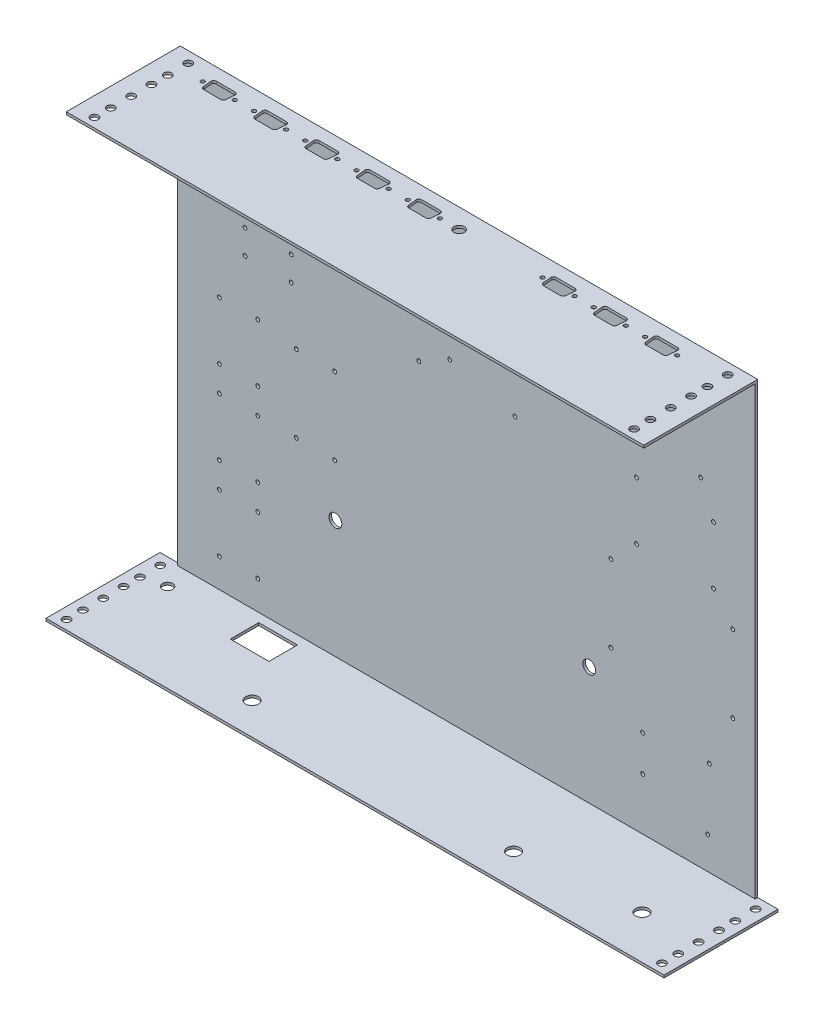
SolidWorks part; units mm, degrees
ref_plane "Front Plane" through (0, 0, 0) normal (0, 0, 1) x (1, 0, 0)
ref_plane "Top Plane" through (0, 0, 0) normal (0, 1, 0) x (1, 0, 0)
ref_plane "Right Plane" through (0, 0, 0) normal (1, 0, 0) x (0, 0, -1)
sketch "Sketch1" plane through (0, 0, 0) normal (0, 0, 1) x (1, 0, 0)
  line L13 (-225.2, -176) -> (225.2, -176)
  line L14 (-225.2, -176) -> (-225.2, 176)
  line L19 (-225.2, 176) -> (225.2, 176)
  line L20 (225.2, -176) -> (225.2, 176)
  line L21 (-225.2, -176) -> (225.2, 176) construction
  line L22 (-225.2, 176) -> (225.2, -176) construction
  point P0 (0, 0)
  dimension "D1" = 450.4
  dimension "D2" = 352
extrude "Boss-Extrude1" add sketch "Sketch1" along normal blind 2
sketch "Sketch4" plane through (0, -176, 0) normal (0, -1, 0) x (1, 0, 0)
  line L0 (-225.2, 2) -> (-225.2, 0) construction
  line L1 (-241, 0) -> (241, 0)
  line L2 (-241, 0) -> (-241, 88.9)
  line L3 (-241, 88.9) -> (241, 88.9)
  line L4 (241, 0) -> (241, 88.9)
  line L5 (225.2, 2) -> (225.2, 0) construction
  line L6 (-227.45, 88.9) -> (-227.45, 0) construction
  line L7 (-236.95, 64.2) -> (-227.45, 64.2)
  line L8 (-236.95, 86.4) -> (-227.45, 86.4)
  line L9 (-236.95, 86.4) -> (-236.95, 76.9)
  line L10 (-236.95, 76.9) -> (-227.45, 76.9)
  line L11 (-227.45, 86.4) -> (-227.45, 76.9)
  line L12 (-236.95, 73.7) -> (-236.95, 64.2)
  line L13 (-236.95, 73.7) -> (-227.45, 73.7)
  line L14 (-227.45, 73.7) -> (-227.45, 64.2)
  line L27 (0, 0) -> (0, 101.053) construction
  line L40 (227.45, 73.7) -> (227.45, 64.2)
  line L41 (236.95, 64.2) -> (227.45, 64.2)
  line L42 (236.95, 73.7) -> (227.45, 73.7)
  line L43 (236.95, 73.7) -> (236.95, 64.2)
  line L44 (227.45, 86.4) -> (227.45, 76.9)
  line L45 (236.95, 86.4) -> (227.45, 86.4)
  line L46 (236.95, 86.4) -> (236.95, 76.9)
  line L47 (236.95, 76.9) -> (227.45, 76.9)
  line L48 (-236.95, 51.5) -> (-227.45, 51.5) [skipped]
  line L49 (-236.95, 61) -> (-236.95, 51.5) [skipped]
  line L50 (-236.95, 61) -> (-227.45, 61) [skipped]
  line L51 (-227.45, 61) -> (-227.45, 51.5) [skipped]
  line L52 (-236.95, 38.8) -> (-227.45, 38.8) [skipped]
  line L53 (-236.95, 48.3) -> (-236.95, 38.8) [skipped]
  line L54 (-236.95, 48.3) -> (-227.45, 48.3) [skipped]
  line L55 (-227.45, 48.3) -> (-227.45, 38.8) [skipped]
  line L56 (-236.95, 26.1) -> (-227.45, 26.1) [skipped]
  line L57 (-236.95, 35.6) -> (-236.95, 26.1) [skipped]
  line L58 (-236.95, 35.6) -> (-227.45, 35.6) [skipped]
  line L59 (-227.45, 35.6) -> (-227.45, 26.1) [skipped]
  line L60 (-236.95, 57.82) -> (-236.95, 48.32)
  line L61 (-236.95, 57.82) -> (-227.45, 57.82)
  line L62 (-227.45, 57.82) -> (-227.45, 48.32)
  line L63 (-236.95, 48.32) -> (-227.45, 48.32)
  line L72 (236.95, 48.32) -> (227.45, 48.32)
  line L73 (227.45, 57.82) -> (227.45, 48.32)
  line L74 (236.95, 57.82) -> (227.45, 57.82)
  line L75 (236.95, 57.82) -> (236.95, 48.32)
  line L92 (-236.95, 45.12) -> (-227.45, 45.12) [skipped]
  line L93 (-227.45, 45.12) -> (-227.45, 35.62) [skipped]
  line L94 (-236.95, 35.62) -> (-227.45, 35.62) [skipped]
  line L95 (-236.95, 45.12) -> (-236.95, 35.62) [skipped]
  line L96 (-236.95, 29.24) -> (-236.95, 19.74) [skipped]
  line L97 (-236.95, 29.24) -> (-227.45, 29.24) [skipped]
  line L98 (-227.45, 29.24) -> (-227.45, 19.74) [skipped]
  line L99 (-236.95, 19.74) -> (-227.45, 19.74) [skipped]
  line L100 (-236.95, 16.54) -> (-227.45, 16.54) [skipped]
  line L101 (-227.45, 16.54) -> (-227.45, 7.04) [skipped]
  line L102 (-236.95, 7.04) -> (-227.45, 7.04) [skipped]
  line L103 (-236.95, 16.54) -> (-236.95, 7.04) [skipped]
  line L104 (236.95, 45.12) -> (236.95, 35.62) [skipped]
  line L105 (236.95, 45.12) -> (227.45, 45.12) [skipped]
  line L106 (227.45, 45.12) -> (227.45, 35.62) [skipped]
  line L107 (236.95, 35.62) -> (227.45, 35.62) [skipped]
  line L108 (236.95, 16.54) -> (236.95, 7.04) [skipped]
  line L109 (236.95, 16.54) -> (227.45, 16.54) [skipped]
  line L110 (227.45, 16.54) -> (227.45, 7.04) [skipped]
  line L111 (236.95, 7.04) -> (227.45, 7.04) [skipped]
  line L112 (236.95, 19.74) -> (227.45, 19.74) [skipped]
  line L113 (227.45, 29.24) -> (227.45, 19.74) [skipped]
  line L114 (236.95, 29.24) -> (227.45, 29.24) [skipped]
  line L115 (236.95, 29.24) -> (236.95, 19.74) [skipped]
  line L116 (-236.95, 41.94) -> (-236.95, 32.44)
  line L117 (-236.95, 41.94) -> (-227.45, 41.94)
  line L118 (-227.45, 41.94) -> (-227.45, 32.44)
  line L119 (-236.95, 32.44) -> (-227.45, 32.44)
  line L120 (-236.95, 29.24) -> (-227.45, 29.24)
  line L121 (-227.45, 29.24) -> (-227.45, 19.74)
  line L122 (-236.95, 19.74) -> (-227.45, 19.74)
  line L123 (-236.95, 29.24) -> (-236.95, 19.74)
  line L124 (-236.95, 13.36) -> (-236.95, 3.86)
  line L125 (-236.95, 3.86) -> (-227.45, 3.86)
  line L126 (-227.45, 13.36) -> (-227.45, 3.86)
  line L127 (-236.95, 13.36) -> (-227.45, 13.36)
  line L128 (227.45, 41.94) -> (227.45, 32.44)
  line L129 (236.95, 32.44) -> (227.45, 32.44)
  line L130 (236.95, 41.94) -> (236.95, 32.44)
  line L131 (236.95, 41.94) -> (227.45, 41.94)
  line L132 (236.95, 29.24) -> (236.95, 19.74)
  line L133 (236.95, 19.74) -> (227.45, 19.74)
  line L134 (227.45, 29.24) -> (227.45, 19.74)
  line L135 (236.95, 29.24) -> (227.45, 29.24)
  line L136 (236.95, 13.36) -> (227.45, 13.36)
  line L137 (236.95, 13.36) -> (236.95, 3.86)
  line L138 (236.95, 3.86) -> (227.45, 3.86)
  line L139 (227.45, 13.36) -> (227.45, 3.86)
  point P21 (-232.2, 57.82)
  dimension "D1" = 15.8
  dimension "D2" = 15.8
  dimension "D3" = 88.9
  dimension "D4" = 2.25
  dimension "D5" = 9.5
  dimension "D6" = 2.5
  dimension "D7" = 9.5
  dimension "D9" = 12.7
  dimension "D11" = 6.38
  dimension "D12" = 2
  dimension "D13" = 6.38
  dimension "D8" = 5
  dimension "D10" = 3
extrude "Boss-Extrude4" add sketch "Sketch4" against normal blind 2
ref_plane "Plane1" through (0, 0, 0) normal (0, 1, 0) x (1, 0, 0)
mirror "Mirror1" about plane through (0, 0, 0) normal (0, 1, 0) of "Boss-Extrude4"
sketch "Sketch5" plane through (0, 176, 0) normal (0, 1, 0) x (1, 0, 0)
  line L0 (-225.2, 0) -> (-225.2, -88.9) construction
  line L1 (241, 0) -> (-241, 0) construction
  line L2 (241, -88.9) -> (-241, -88.9) construction
  line L7 (0, -48.895) -> (0, 48.895) construction
  line L11 (-225.2, 0) -> (-241, 0)
  line L12 (-225.2, 0) -> (-225.2, -88.9)
  line L13 (-225.2, -88.9) -> (-241, -88.9)
  line L14 (-241, 0) -> (-241, -88.9)
  line L15 (225.2, 0) -> (241, 0)
  line L16 (241, 0) -> (241, -88.9)
  line L17 (225.2, -88.9) -> (241, -88.9)
  line L18 (225.2, 0) -> (225.2, -88.9)
extrude "Cut-Extrude2" cut sketch "Sketch5" against normal up to next
sketch "Sketch6" plane through (0, 176, 0) normal (0, 1, 0) x (1, 0, 0)
  line L0 (-225.2, -88.9) -> (-225.2, 0) construction
  line L1 (-215.2, -3.86) -> (-205.7, -3.86)
  line L2 (-215.2, -3.86) -> (-215.2, -13.36)
  line L3 (-215.2, -13.36) -> (-205.7, -13.36)
  line L4 (-205.7, -3.86) -> (-205.7, -13.36)
  line L5 (225.2, 0) -> (-225.2, 0) construction
  line L6 (-215.2, -19.74) -> (-215.2, -29.24)
  line L7 (-215.2, -19.74) -> (-205.7, -19.74)
  line L8 (-215.2, -29.24) -> (-205.7, -29.24)
  line L9 (-205.7, -19.74) -> (-205.7, -29.24)
  line L22 (0, -48.895) -> (0, 48.895) construction
  line L35 (215.2, -3.86) -> (215.2, -13.36)
  line L36 (215.2, -3.86) -> (205.7, -3.86)
  line L37 (205.7, -3.86) -> (205.7, -13.36)
  line L38 (215.2, -13.36) -> (205.7, -13.36)
  line L39 (215.2, -19.74) -> (215.2, -29.24)
  line L40 (215.2, -29.24) -> (205.7, -29.24)
  line L41 (205.7, -19.74) -> (205.7, -29.24)
  line L42 (215.2, -19.74) -> (205.7, -19.74)
  line L43 (-215.2, -76.9) -> (-215.2, -86.4)
  line L44 (-215.2, -35.62) -> (-215.2, -45.12) [skipped]
  line L45 (-215.2, -35.62) -> (-205.7, -35.62) [skipped]
  line L46 (-215.2, -45.12) -> (-205.7, -45.12) [skipped]
  line L47 (-205.7, -35.62) -> (-205.7, -45.12) [skipped]
  line L48 (-215.2, -51.5) -> (-215.2, -61) [skipped]
  line L49 (-215.2, -51.5) -> (-205.7, -51.5) [skipped]
  line L50 (-215.2, -61) -> (-205.7, -61) [skipped]
  line L51 (-205.7, -51.5) -> (-205.7, -61) [skipped]
  line L52 (-215.2, -67.38) -> (-215.2, -76.88) [skipped]
  line L53 (-215.2, -67.38) -> (-205.7, -67.38) [skipped]
  line L54 (-205.7, -67.38) -> (-205.7, -76.88) [skipped]
  line L55 (-215.2, -76.88) -> (-205.7, -76.88) [skipped]
  line L56 (-215.2, -32.44) -> (-215.2, -41.94)
  line L57 (-215.2, -41.94) -> (-205.7, -41.94)
  line L58 (-215.2, -32.44) -> (-205.7, -32.44)
  line L63 (-205.7, -32.44) -> (-205.7, -41.94)
  line L64 (205.7, -32.44) -> (205.7, -41.94)
  line L65 (215.2, -41.94) -> (205.7, -41.94)
  line L66 (215.2, -32.44) -> (215.2, -41.94)
  line L67 (215.2, -32.44) -> (205.7, -32.44)
  line L88 (-215.2, -48.32) -> (-205.7, -48.32) [skipped]
  line L89 (-215.2, -48.32) -> (-215.2, -57.82) [skipped]
  line L90 (-215.2, -57.82) -> (-205.7, -57.82) [skipped]
  line L91 (-205.7, -48.32) -> (-205.7, -57.82) [skipped]
  line L92 (-215.2, -61.02) -> (-215.2, -70.52) [skipped]
  line L93 (-215.2, -70.52) -> (-205.7, -70.52) [skipped]
  line L94 (-215.2, -61.02) -> (-205.7, -61.02) [skipped]
  line L95 (-215.2, -76.9) -> (-205.7, -76.9) [skipped]
  line L96 (-215.2, -76.9) -> (-215.2, -86.4) [skipped]
  line L97 (-215.2, -86.4) -> (-205.7, -86.4) [skipped]
  line L98 (-205.7, -76.9) -> (-205.7, -86.4) [skipped]
  line L99 (-205.7, -61.02) -> (-205.7, -70.52) [skipped]
  line L100 (215.2, -57.82) -> (205.7, -57.82) [skipped]
  line L101 (205.7, -48.32) -> (205.7, -57.82) [skipped]
  line L102 (215.2, -48.32) -> (205.7, -48.32) [skipped]
  line L103 (215.2, -48.32) -> (215.2, -57.82) [skipped]
  line L104 (205.7, -61.02) -> (205.7, -70.52) [skipped]
  line L105 (215.2, -70.52) -> (205.7, -70.52) [skipped]
  line L106 (215.2, -61.02) -> (215.2, -70.52) [skipped]
  line L107 (215.2, -61.02) -> (205.7, -61.02) [skipped]
  line L108 (215.2, -86.4) -> (205.7, -86.4) [skipped]
  line L109 (205.7, -76.9) -> (205.7, -86.4) [skipped]
  line L110 (215.2, -76.9) -> (205.7, -76.9) [skipped]
  line L111 (215.2, -76.9) -> (215.2, -86.4) [skipped]
  line L112 (-215.2, -76.9) -> (-205.7, -76.9)
  line L113 (-215.2, -86.4) -> (-205.7, -86.4)
  line L114 (-205.7, -76.9) -> (-205.7, -86.4)
  line L115 (-205.7, -64.2) -> (-205.7, -73.7)
  line L116 (-215.2, -73.7) -> (-205.7, -73.7)
  line L117 (-215.2, -64.2) -> (-215.2, -73.7)
  line L118 (-215.2, -64.2) -> (-205.7, -64.2)
  line L119 (-215.2, -57.82) -> (-205.7, -57.82)
  line L120 (-215.2, -48.32) -> (-215.2, -57.82)
  line L121 (-215.2, -48.32) -> (-205.7, -48.32)
  line L122 (-205.7, -48.32) -> (-205.7, -57.82)
  line L123 (205.7, -48.32) -> (205.7, -57.82)
  line L124 (215.2, -57.82) -> (205.7, -57.82)
  line L125 (215.2, -48.32) -> (215.2, -57.82)
  line L126 (215.2, -48.32) -> (205.7, -48.32)
  line L127 (215.2, -64.2) -> (205.7, -64.2)
  line L128 (215.2, -64.2) -> (215.2, -73.7)
  line L129 (215.2, -73.7) -> (205.7, -73.7)
  line L130 (205.7, -64.2) -> (205.7, -73.7)
  line L131 (215.2, -76.9) -> (205.7, -76.9)
  line L132 (205.7, -76.9) -> (205.7, -86.4)
  line L133 (215.2, -86.4) -> (205.7, -86.4)
  line L134 (215.2, -76.9) -> (215.2, -86.4)
  dimension "D1" = 9.5
  dimension "D2" = 9.5
  dimension "D3" = 10
  dimension "D4" = 3.86
  dimension "D6" = 6.38
  dimension "D8" = 3.2
  dimension "D10" = 6.38
  dimension "D5" = 5
  dimension "D7" = 3
  dimension "D9" = 2
extrude "Cut-Extrude3" cut sketch "Sketch6" against normal up to next
sketch "Sketch9" plane through (0, 0, 2) normal (0, 0, 1) x (1, 0, 0)
  line L0 (-87.2, -174) -> (-87.2, 8) construction
  line L1 (241, -174) -> (-241, -174) construction
  line L2 (80.8, -174) -> (80.8, 8) construction
  line L3 (-225.2, -174) -> (225.2, -174) construction
  line L4 (-87.2, 8) -> (80.8, 8) construction
  line L5 (-225.2, 174) -> (-225.2, -174) construction
  circle A0 centre (-102.2, -82) radius 5
  circle A3 centre (95.8, -82) radius 5
  dimension "D4" = 15
  dimension "D5" = 10
  dimension "D6" = 10
  dimension "D1" = 138
  dimension "D2" = 168
  dimension "D3" = 182
  dimension "D8" = 15
  dimension "D9" = 90
  dimension "D15" = 90
extrude "Cut-Extrude4" cut sketch "Sketch9" against normal up to next
sketch "Sketch11" plane through (0, -176, 0) normal (0, -1, 0) x (1, 0, 0)
  line L0 (-90.2, 0) -> (-90.2, 85.1375) construction
  line L1 (-241, 0) -> (241, 0) construction
  line L2 (83.8, 0) -> (83.8, 87.0276) construction
  line L10 (-241, 88.9) -> (-241, 0) construction
  line L11 (-90.2, 79) -> (83.8, 79) construction
  circle A0 centre (-105.2, 64) radius 5
  circle A1 centre (98.8, 64) radius 5
  dimension "D4" = 10
  dimension "D5" = 10
  dimension "D1" = 174
  dimension "D2" = 150.8
  dimension "D3" = 79
  dimension "D6" = 15
  dimension "D7" = 15
  dimension "D8" = 15
  dimension "D9" = 15
extrude "Cut-Extrude5" cut sketch "Sketch11" against normal up to next
sketch "Sketch12" plane through (0, 0, 2) normal (0, 0, 1) x (1, 0, 0)
  line L0 (-225.2, -174) -> (225.2, -174) construction
  line L1 (-195.2, -154) -> (-160.2, -154)
  line L2 (-195.2, -154) -> (-195.2, -104)
  line L3 (-195.2, -104) -> (-160.2, -104)
  line L4 (-160.2, -154) -> (-160.2, -104)
  line L5 (-195.2, -154) -> (-160.2, -104) construction
  line L6 (-195.2, -104) -> (-160.2, -154) construction
  line L7 (-225.2, 174) -> (-225.2, -174) construction
  line L12 (-195.2, -89) -> (-160.2, -89)
  line L13 (-195.2, -89) -> (-195.2, -39)
  line L18 (-195.2, -39) -> (-160.2, -39)
  line L19 (-160.2, -89) -> (-160.2, -39)
  line L20 (-195.2, -104) -> (-195.2, 47.085) construction
  line L21 (-195.2, -89) -> (-160.2, -39) construction
  line L22 (-195.2, -39) -> (-160.2, -89) construction
  line L23 (-195.2, -24) -> (-160.2, -24)
  line L24 (-195.2, -24) -> (-195.2, 26)
  line L25 (-195.2, 26) -> (-160.2, 26)
  line L26 (-160.2, -24) -> (-160.2, 26)
  line L27 (-195.2, -24) -> (-160.2, 26) construction
  line L28 (-195.2, 26) -> (-160.2, -24) construction
  line L30 (-135.2, 21) -> (-100.2, 21)
  line L31 (-135.2, 21) -> (-135.2, -44)
  line L32 (-135.2, -44) -> (-100.2, -44)
  line L33 (-100.2, 21) -> (-100.2, -44)
  line L34 (-117.7, -44) -> (-117.7, 21) construction
  line L35 (-135.2, -11.5) -> (-100.2, -11.5) construction
  circle A0 centre (-192.7, -151.5) radius 1.5
  circle A1 centre (-162.7, -151.5) radius 1.5
  circle A2 centre (-162.7, -106.5) radius 1.5
  circle A3 centre (-192.7, -106.5) radius 1.5
  circle A12 centre (-192.7, -86.5) radius 1.5
  circle A13 centre (-162.7, -86.5) radius 1.5
  circle A14 centre (-162.7, -41.5) radius 1.5
  circle A15 centre (-192.7, -41.5) radius 1.5
  circle A16 centre (-192.7, -21.5) radius 1.5
  circle A17 centre (-162.7, -21.5) radius 1.5
  circle A18 centre (-162.7, 23.5) radius 1.5
  circle A19 centre (-192.7, 23.5) radius 1.5
  circle A20 centre (-132.7, 18.5) radius 1.5
  circle A21 centre (-102.7, 18.5) radius 1.5
  circle A22 centre (-102.7, -41.5) radius 1.5
  circle A23 centre (-132.7, -41.5) radius 1.5
  point P4 (-177.7, -129)
  point P21 (-177.7, -64)
  point P34 (-177.7, 1)
  point P205 (-117.7, -11.5)
  dimension "D7" = 3
  dimension "D8" = 3
  dimension "D13" = 3
  dimension "D16" = 3
  dimension "D19" = 2.5
  dimension "D22" = 3
  dimension "D20" = 3
  dimension "D27" = 3
  dimension "D30" = 3
  dimension "D34" = 3
  dimension "D36" = 3
  dimension "D41" = 3
  dimension "D44" = 3
  dimension "D51" = 3
  dimension "D52" = 3
  dimension "D53" = 3
  dimension "D54" = 3
  dimension "D1" = 20
  dimension "D2" = 30
  dimension "D3" = 35
  dimension "D4" = 50
  dimension "D5" = 2.5
  dimension "D6" = 2.5
  dimension "D9" = 2.5
  dimension "D10" = 2.5
  dimension "D11" = 2.5
  dimension "D12" = 2.5
  dimension "D14" = 2.5
  dimension "D15" = 2.5
  dimension "D17" = 35
  dimension "D18" = 50
  dimension "D21" = 2.5
  dimension "D23" = 2.5
  dimension "D24" = 2.5
  dimension "D25" = 2.5
  dimension "D26" = 2.5
  dimension "D28" = 2.5
  dimension "D29" = 2.5
  dimension "D31" = 35
  dimension "D32" = 50
  dimension "D33" = 2.5
  dimension "D35" = 2.5
  dimension "D37" = 2.5
  dimension "D38" = 2.5
  dimension "D39" = 2.5
  dimension "D40" = 2.5
  dimension "D42" = 2.5
  dimension "D43" = 2.5
  dimension "D45" = 15
  dimension "D46" = 15
  dimension "D47" = 35
  dimension "D48" = 65
  dimension "D49" = 25
  dimension "D55" = 2.5
  dimension "D56" = 2.5
  dimension "D57" = 2.5
  dimension "D58" = 2.5
  dimension "D59" = 2.5
  dimension "D60" = 2.5
  dimension "D61" = 2.5
  dimension "D62" = 2.5
extrude "Cut-Extrude6" cut sketch "Sketch12" against normal blind 30 contours A0 | A1 | A12 | A13 | A15 | A14 | A16 | A3 | A2 | A17 | A23 | A22 | A20 | A21 | A18 | A19
sketch "Sketch15" plane through (0, 0, 2) normal (0, 0, 1) x (1, 0, 0)
  line L0 (39.08, 106.761) -> (-43.398, 106.761) construction
  line L1 (-175.2, 59) -> (-134.2, 59)
  line L2 (-175.2, 59) -> (-175.2, 83)
  line L3 (-175.2, 83) -> (-134.2, 83)
  line L4 (-134.2, 59) -> (-134.2, 83)
  line L5 (-154.7, 83) -> (-154.7, 59) construction
  line L6 (-175.2, 71) -> (-134.2, 71) construction
  line L7 (-60.2, 119) -> (59.8, 119)
  line L8 (-60.2, 119) -> (-60.2, 46)
  line L9 (-60.2, 46) -> (59.8, 46)
  line L10 (59.8, 119) -> (59.8, 46)
  line L11 (-0.2, 46) -> (-0.2, 119) construction
  line L12 (-60.2, 82.5) -> (59.8, 82.5) construction
  line L13 (90.2, 139) -> (185.2, 139)
  line L14 (90.2, 139) -> (90.2, 87)
  line L15 (90.2, 87) -> (185.2, 87)
  line L16 (185.2, 139) -> (185.2, 87)
  line L17 (137.7, 87) -> (137.7, 139) construction
  line L18 (90.2, 113) -> (185.2, 113) construction
  line L19 (130.2, 67) -> (195.2, 67)
  line L20 (130.2, 67) -> (130.2, 17)
  line L21 (130.2, 17) -> (195.2, 17)
  line L22 (195.2, 67) -> (195.2, 17)
  line L23 (162.7, 17) -> (162.7, 67) construction
  line L24 (130.2, 42) -> (195.2, 42) construction
  line L25 (110.2, 2) -> (210.2, 2)
  line L26 (110.2, 2) -> (110.2, -63)
  line L27 (110.2, -63) -> (210.2, -63)
  line L28 (210.2, 2) -> (210.2, -63)
  line L29 (160.2, -63) -> (160.2, 2) construction
  line L30 (110.2, -30.5) -> (210.2, -30.5) construction
  line L31 (134.925, -88) -> (210.2, -88)
  line L32 (134.925, -88) -> (134.925, -161)
  line L33 (134.925, -161) -> (210.2, -161)
  line L34 (210.2, -88) -> (210.2, -161)
  line L35 (172.5625, -161) -> (172.5625, -88) construction
  line L36 (134.925, -124.5) -> (210.2, -124.5) construction
  line L41 (-225.2, 174) -> (-225.2, -174) construction
  line L42 (225.2, 174) -> (-225.2, 174) construction
  line L43 (225.2, -174) -> (225.2, 174) construction
  line L44 (92.7, 89.5) -> (182.7, 89.5)
  line L45 (-172.7, 61.5) -> (-136.7, 61.5)
  line L46 (-172.7, 61.5) -> (-172.7, 80.5)
  line L47 (-172.7, 80.5) -> (-136.7, 80.5)
  line L48 (-136.7, 61.5) -> (-136.7, 80.5)
  line L49 (-172.7, 61.5) -> (-136.7, 80.5) construction
  line L50 (-172.7, 80.5) -> (-136.7, 61.5) construction
  line L51 (92.7, 89.5) -> (92.7, 136.5)
  line L52 (92.7, 136.5) -> (182.7, 136.5)
  line L53 (182.7, 89.5) -> (182.7, 136.5)
  line L54 (92.7, 89.5) -> (182.7, 136.5) construction
  line L55 (92.7, 136.5) -> (182.7, 89.5) construction
  line L56 (132.7, 19.5) -> (192.7, 19.5)
  line L57 (132.7, 19.5) -> (132.7, 64.5)
  line L58 (132.7, 64.5) -> (192.7, 64.5)
  line L59 (192.7, 19.5) -> (192.7, 64.5)
  line L60 (132.7, 19.5) -> (192.7, 64.5) construction
  line L61 (132.7, 64.5) -> (192.7, 19.5) construction
  line L62 (112.7, -60.5) -> (207.7, -60.5)
  line L63 (112.7, -60.5) -> (112.7, -0.5)
  line L64 (112.7, -0.5) -> (207.7, -0.5)
  line L65 (207.7, -60.5) -> (207.7, -0.5)
  line L66 (112.7, -60.5) -> (207.7, -0.5) construction
  line L67 (112.7, -0.5) -> (207.7, -60.5) construction
  line L68 (-48.55, 55.7) -> (59.8, 55.7)
  line L69 (-48.55, 55.7) -> (-48.55, 109.3)
  line L70 (-48.55, 109.3) -> (59.8, 109.3)
  line L71 (59.8, 55.7) -> (59.8, 109.3)
  line L72 (5.625, 109.3) -> (5.625, 55.7) construction
  line L73 (-48.55, 82.5) -> (59.8, 82.5) construction
  line L74 (-12.95, 106.761) -> (-12.95, 55.7) construction
  line L75 (137.45, -97.85) -> (137.45, -151.15) construction
  line L76 (134.92, -151.15) -> (210.2, -151.15)
  line L77 (134.92, -151.15) -> (134.92, -97.85)
  line L78 (134.92, -97.85) -> (210.2, -97.85)
  line L79 (210.2, -151.15) -> (210.2, -97.85)
  line L80 (172.56, -97.85) -> (172.56, -151.15) construction
  line L81 (134.92, -124.5) -> (210.2, -124.5) construction
  circle A0 centre (-172.7, 80.5) radius 1.4993
  circle A1 centre (-172.7, 61.5) radius 1.5
  circle A2 centre (-136.7, 61.5) radius 1.5
  circle A3 centre (-136.7, 80.5) radius 1.5
  circle A4 centre (112.7, -0.5) radius 1.5
  circle A5 centre (112.7, -60.5) radius 1.5
  circle A6 centre (207.7, -60.5) radius 1.5
  circle A7 centre (207.7, -0.5) radius 1.5
  circle A8 centre (132.7, 64.5) radius 1.5
  circle A9 centre (132.7, 19.5) radius 1.5
  circle A10 centre (192.7, 19.5) radius 1.5
  circle A11 centre (192.7, 64.5) radius 1.5
  circle A12 centre (92.7, 136.5) radius 1.5
  circle A13 centre (92.7, 89.5) radius 1.5
  circle A14 centre (182.7, 89.5) radius 1.5
  circle A15 centre (182.7, 136.5) radius 1.5
  circle A16 centre (39.08, 106.761) radius 1.5
  circle A17 centre (-43.398, 106.761) radius 1.5
  circle A18 centre (-37.145, 58.239) radius 1.5
  circle A19 centre (37.81, 58.239) radius 1.5
  circle A20 centre (-12.95, 99.144) radius 1.5
  circle A21 centre (-12.95, 71.235) radius 1.5
  circle A22 centre (189.48, -100.389) radius 1.5
  circle A23 centre (188.215, -148.911) radius 1.5
  circle A24 centre (137.45, -105.467) radius 1.5
  circle A25 centre (137.45, -133.376) radius 1.5
  point P30 (-154.7, 71)
  point P39 (137.7, 113)
  point P44 (162.7, 42)
  point P49 (160.2, -30.5)
  point P124 (172.5625, -124.5)
  point P152 (-0.2, 82.5)
  point P164 (-154.7, 71)
  point P194 (160.2, -30.5)
  point P246 (137.7, 113)
  point P275 (162.7, 42)
  point P395 (172.56, -124.5)
  point P605 (5.625, 82.5)
  dimension "D27" = 2.9987
  dimension "D28" = 3
  dimension "D29" = 3
  dimension "D30" = 3
  dimension "D33" = 3
  dimension "D34" = 3
  dimension "D35" = 3
  dimension "D36" = 3
  dimension "D39" = 3
  dimension "D40" = 3
  dimension "D41" = 3
  dimension "D42" = 3
  dimension "D45" = 3
  dimension "D46" = 3
  dimension "D47" = 3
  dimension "D48" = 3
  dimension "D52" = 3
  dimension "D57" = 3
  dimension "D58" = 3
  dimension "D59" = 3
  dimension "D66" = 3
  dimension "D67" = 3
  dimension "D71" = 3
  dimension "D72" = 3
  dimension "D78" = 3
  dimension "D79" = 3
  dimension "D1" = 50
  dimension "D2" = 115
  dimension "D3" = 24
  dimension "D4" = 41
  dimension "D5" = 73
  dimension "D6" = 120
  dimension "D7" = 73
  dimension "D8" = 75.275
  dimension "D9" = 52
  dimension "D10" = 95
  dimension "D11" = 50
  dimension "D12" = 65
  dimension "D13" = 65
  dimension "D14" = 100
  dimension "D15" = 55
  dimension "D16" = 165
  dimension "D17" = 35
  dimension "D18" = 40
  dimension "D19" = 20
  dimension "D20" = 30
  dimension "D21" = 15
  dimension "D22" = 15
  dimension "D23" = 15
  dimension "D24" = 25
  dimension "D25" = 2.5
  dimension "D26" = 2.5
  dimension "D31" = 2.5
  dimension "D32" = 2.5
  dimension "D37" = 2.5
  dimension "D38" = 2.5
  dimension "D43" = 2.5
  dimension "D44" = 2.5
  dimension "D49" = 53.6
  dimension "D50" = 108.35
  dimension "D51" = 0
  dimension "D53" = 2.539
  dimension "D54" = 20.72
  dimension "D55" = 82.478
  dimension "D56" = 48.522
  dimension "D60" = 48.522
  dimension "D61" = 21.99
  dimension "D62" = 11.405
  dimension "D63" = 52.03
  dimension "D64" = 7.617
  dimension "D65" = 27.909
  dimension "D68" = 75.28
  dimension "D69" = 53.3
  dimension "D70" = 0
  dimension "D73" = 20.72
  dimension "D74" = 2.539
  dimension "D75" = 21.985
  dimension "D76" = 48.522
  dimension "D77" = 52.03
  dimension "D80" = 27.909
  dimension "D81" = 7.617
extrude "Cut-Extrude7" cut sketch "Sketch15" against normal up to next (2 mm away) contours A2 | A1 | A0 | A3 | A17 | A18 | A21 | A20 | A19 | A16 | A12 | A13 | A14 | A15 | A9 | A8 | A11 | A10 | A4 | A5 | A7 | A6 | A25 | A24 | A22 | A23
sketch "Sketch16" plane through (0, 176, 0) normal (0, 1, 0) x (1, 0, 0)
  line L0 (-200.0189, -15) -> (190.2231, -15) construction
  line L2 (-147.3524, -9.7) -> (-132.6476, -9.7)
  line L4 (-140, -28.7384) -> (-140, -16.1884) construction
  line L5 (-146.7298, -20.3) -> (-133.2702, -20.3)
  line L8 (-130.45, -9.7) -> (-130.45, -26.4134) construction
  line L9 (225.2, 0) -> (-225.2, 0) construction
  line L10 (-107.3479, -9.7) -> (-92.643, -9.7)
  line L23 (-149.55, -9.7) -> (-149.55, -23.1825) construction
  line L25 (-130.6564, -11.8878) -> (-131.279, -18.4878)
  line L27 (-149.3436, -11.8878) -> (-148.721, -18.4878)
  line L28 (-149.55, -9.7) -> (-149.55, -9.1639) construction
  line L29 (-90.6518, -11.8878) -> (-91.2745, -18.4878)
  line L30 (-106.7252, -20.3) -> (-93.2656, -20.3)
  line L31 (-109.339, -11.8878) -> (-108.7164, -18.4878)
  line L32 (-67.3433, -9.7) -> (-52.6384, -9.7)
  line L33 (-50.6473, -11.8878) -> (-51.2699, -18.4878)
  line L34 (-66.7207, -20.3) -> (-53.2611, -20.3)
  line L35 (-69.3345, -11.8878) -> (-68.7118, -18.4878)
  line L36 (-27.3388, -9.7) -> (-12.6339, -9.7)
  line L37 (-10.6427, -11.8878) -> (-11.2654, -18.4878)
  line L38 (-26.7161, -20.3) -> (-13.2565, -20.3)
  line L39 (-29.3299, -11.8878) -> (-28.7073, -18.4878)
  line L44 (-187.357, -9.7) -> (-172.6521, -9.7)
  line L45 (-189.3482, -11.8878) -> (-188.7255, -18.4878)
  line L50 (78.2793, -20.3) -> (91.7389, -20.3)
  line L51 (75.6655, -11.8878) -> (76.2882, -18.4878)
  line L56 (77.6567, -9.7) -> (92.3616, -9.7)
  line L57 (94.3527, -11.8878) -> (93.7301, -18.4878)
  line L62 (118.2839, -20.3) -> (131.7435, -20.3)
  line L63 (115.6701, -11.8878) -> (116.2927, -18.4878)
  line L64 (-186.7344, -20.3) -> (-173.2748, -20.3)
  line L65 (-170.661, -11.8878) -> (-171.2836, -18.4878)
  line L66 (117.6612, -9.7) -> (132.3661, -9.7)
  line L67 (134.3573, -11.8878) -> (133.7346, -18.4878)
  line L72 (155.6746, -11.8878) -> (156.2973, -18.4878) [skipped]
  line L73 (157.6658, -9.7) -> (172.3707, -9.7) [skipped]
  line L74 (158.2884, -20.3) -> (171.748, -20.3) [skipped]
  line L75 (174.3618, -11.8878) -> (173.7392, -18.4878) [skipped]
  line L76 (158.2884, -20.3) -> (171.748, -20.3)
  line L77 (155.6746, -11.8878) -> (156.2973, -18.4878)
  line L78 (157.6658, -9.7) -> (172.3707, -9.7)
  line L79 (174.3618, -11.8878) -> (173.7392, -18.4878)
  arc A31 (-131.279, -18.4878) -> (-133.2702, -20.3) centre (-133.2702, -18.3) cw
  arc A32 (-146.7298, -20.3) -> (-148.721, -18.4878) centre (-146.7298, -18.3) cw
  arc A33 (-130.6564, -11.8878) -> (-132.6476, -9.7) centre (-132.6476, -11.7) ccw
  arc A34 (-149.3436, -11.8878) -> (-147.3524, -9.7) centre (-147.3524, -11.7) cw
  circle A35 centre (-152.5023, -15.1878) radius 1.5
  circle A36 centre (-127.4977, -15.1878) radius 1.5
  arc A37 (-90.6518, -11.8878) -> (-92.643, -9.7) centre (-92.643, -11.7) ccw
  arc A38 (-91.2745, -18.4878) -> (-93.2656, -20.3) centre (-93.2656, -18.3) cw
  arc A39 (-106.7252, -20.3) -> (-108.7164, -18.4878) centre (-106.7252, -18.3) cw
  arc A40 (-109.339, -11.8878) -> (-107.3479, -9.7) centre (-107.3479, -11.7) cw
  circle A41 centre (-112.4977, -15.1878) radius 1.5
  circle A42 centre (-87.4932, -15.1878) radius 1.5
  arc A43 (-50.6473, -11.8878) -> (-52.6384, -9.7) centre (-52.6384, -11.7) ccw
  arc A44 (-51.2699, -18.4878) -> (-53.2611, -20.3) centre (-53.2611, -18.3) cw
  arc A45 (-66.7207, -20.3) -> (-68.7118, -18.4878) centre (-66.7207, -18.3) cw
  arc A46 (-69.3345, -11.8878) -> (-67.3433, -9.7) centre (-67.3433, -11.7) cw
  circle A47 centre (-72.4932, -15.1878) radius 1.5
  circle A48 centre (-47.4886, -15.1878) radius 1.5
  arc A49 (-10.6427, -11.8878) -> (-12.6339, -9.7) centre (-12.6339, -11.7) ccw
  arc A50 (-11.2654, -18.4878) -> (-13.2565, -20.3) centre (-13.2565, -18.3) cw
  arc A51 (-26.7161, -20.3) -> (-28.7073, -18.4878) centre (-26.7161, -18.3) cw
  arc A52 (-29.3299, -11.8878) -> (-27.3388, -9.7) centre (-27.3388, -11.7) cw
  circle A53 centre (-32.4886, -15.1878) radius 1.5
  circle A54 centre (-7.484, -15.1878) radius 1.5
  circle A55 centre (7.516, -15.1878) radius 4
  circle A72 centre (-192.5068, -15.1878) radius 1.5
  arc A73 (-189.3482, -11.8878) -> (-187.357, -9.7) centre (-187.357, -11.7) cw
  arc A74 (-186.7344, -20.3) -> (-188.7255, -18.4878) centre (-186.7344, -18.3) cw
  arc A75 (-171.2836, -18.4878) -> (-173.2748, -20.3) centre (-173.2748, -18.3) cw
  arc A76 (-170.661, -11.8878) -> (-172.6521, -9.7) centre (-172.6521, -11.7) ccw
  circle A77 centre (-167.5023, -15.1878) radius 1.5
  arc A78 (78.2793, -20.3) -> (76.2882, -18.4878) centre (78.2793, -18.3) cw
  arc A79 (75.6655, -11.8878) -> (77.6567, -9.7) centre (77.6567, -11.7) cw
  arc A80 (94.3527, -11.8878) -> (92.3616, -9.7) centre (92.3616, -11.7) ccw
  arc A81 (93.7301, -18.4878) -> (91.7389, -20.3) centre (91.7389, -18.3) cw
  circle A82 centre (97.5114, -15.1878) radius 1.5
  circle A83 centre (72.5068, -15.1878) radius 1.5
  circle A84 centre (112.5114, -15.1878) radius 1.5
  arc A85 (118.2839, -20.3) -> (116.2927, -18.4878) centre (118.2839, -18.3) cw
  arc A86 (115.6701, -11.8878) -> (117.6612, -9.7) centre (117.6612, -11.7) cw
  arc A87 (134.3573, -11.8878) -> (132.3661, -9.7) centre (132.3661, -11.7) ccw
  arc A88 (133.7346, -18.4878) -> (131.7435, -20.3) centre (131.7435, -18.3) cw
  circle A89 centre (137.516, -15.1878) radius 1.5
  circle A95 centre (152.516, -15.1878) radius 1.5 [skipped]
  arc A96 (155.6746, -11.8878) -> (157.6658, -9.7) centre (157.6658, -11.7) cw [skipped]
  arc A97 (158.2884, -20.3) -> (156.2973, -18.4878) centre (158.2884, -18.3) cw [skipped]
  arc A98 (173.7392, -18.4878) -> (171.748, -20.3) centre (171.748, -18.3) cw [skipped]
  arc A99 (174.3618, -11.8878) -> (172.3707, -9.7) centre (172.3707, -11.7) ccw [skipped]
  circle A100 centre (152.516, -15.1878) radius 1.5
  arc A101 (158.2884, -20.3) -> (156.2973, -18.4878) centre (158.2884, -18.3) cw
  arc A102 (155.6746, -11.8878) -> (157.6658, -9.7) centre (157.6658, -11.7) cw
  arc A103 (174.3618, -11.8878) -> (172.3707, -9.7) centre (172.3707, -11.7) ccw
  arc A104 (173.7392, -18.4878) -> (171.748, -20.3) centre (171.748, -18.3) cw
  circle A105 centre (177.5205, -15.1878) radius 1.5
  point P6 (-140, -9.7)
  point P10 (-149.0323, -15.1878)
  point P12 (-130.9677, -15.1878)
  dimension "D5" = 2
  dimension "D8" = 7.3524
  dimension "D9" = 3
  dimension "D13" = 0.1878
  dimension "D16" = 8
  dimension "D22" = 160
  dimension "D10" = 3
  dimension "D20" = 15
  dimension "D24" = 15
  dimension "D1" = 5.3
  dimension "D2" = 19.1
  dimension "D3" = 5.3
  dimension "D4" = 5.389
  dimension "D6" = 15
  dimension "D7" = 140
  dimension "D11" = 3.47
  dimension "D12" = 3.47
  dimension "D15" = 15
  dimension "D17" = 15
  dimension "D18" = 4
  dimension "D19" = 2
  dimension "D21" = 2
  dimension "D14" = 0.1878
  dimension "D23" = 2
extrude "Cut-Extrude9" cut sketch "Sketch16" against normal up to next (2 mm away)
sketch "Sketch17" plane through (0, -176, 0) normal (0, -1, 0) x (1, 0, 0)
  line L0 (-241, 0) -> (241, 0) construction
  line L1 (-155.1, 31.1) -> (-124.9, 31.1)
  line L2 (-155.1, 31.1) -> (-155.1, 8.9)
  line L3 (-155.1, 8.9) -> (-124.9, 8.9)
  line L4 (-124.9, 31.1) -> (-124.9, 8.9)
  line L5 (-155.1, 31.1) -> (-124.9, 8.9) construction
  line L6 (-155.1, 8.9) -> (-124.9, 31.1) construction
  circle A0 centre (-215.1, 20) radius 4
  circle A1 centre (190, 55) radius 5
  point P0 (-140, 20)
  dimension "D5" = 8
  dimension "D7" = 10
  dimension "D1" = 22.2
  dimension "D2" = 30.2
  dimension "D3" = 140
  dimension "D4" = 20
  dimension "D6" = 60
  dimension "D8" = 55
  dimension "D9" = 190
extrude "Cut-Extrude10" cut sketch "Sketch17" against normal up to next
sketch "Sketch18" plane through (0, -176, 0) normal (0, -1, 0) x (1, 0, 0)
  line L0 (-236.95, 73.7) -> (-227.45, 73.7)
  line L1 (-236.95, 86.4) -> (-227.45, 86.4)
  line L2 (-236.95, 86.4) -> (-236.95, 76.9)
  line L3 (-236.95, 76.9) -> (-227.45, 76.9)
  line L4 (-227.45, 86.4) -> (-227.45, 76.9)
  line L5 (-232.2, 76.9) -> (-232.2, 86.4) construction
  line L6 (-236.95, 81.65) -> (-227.45, 81.65) construction
  line L7 (-236.95, 73.7) -> (-236.95, 64.2)
  line L8 (-236.95, 64.2) -> (-227.45, 64.2)
  line L9 (-227.45, 73.7) -> (-227.45, 64.2)
  line L10 (-232.2, 64.2) -> (-232.2, 73.7) construction
  line L11 (-236.95, 68.95) -> (-227.45, 68.95) construction
  line L12 (-236.95, 57.82) -> (-227.45, 57.82)
  line L13 (-236.95, 57.82) -> (-236.95, 48.32)
  line L14 (-236.95, 48.32) -> (-227.45, 48.32)
  line L15 (-227.45, 57.82) -> (-227.45, 48.32)
  line L16 (-232.2, 48.32) -> (-232.2, 57.82) construction
  line L17 (-236.95, 53.07) -> (-227.45, 53.07) construction
  line L18 (-236.95, 41.94) -> (-227.45, 41.94)
  line L19 (-236.95, 41.94) -> (-236.95, 32.44)
  line L20 (-236.95, 32.44) -> (-227.45, 32.44)
  line L21 (-227.45, 41.94) -> (-227.45, 32.44)
  line L22 (-232.2, 32.44) -> (-232.2, 41.94) construction
  line L23 (-236.95, 37.19) -> (-227.45, 37.19) construction
  line L24 (-236.95, 29.24) -> (-227.45, 29.24)
  line L25 (-236.95, 29.24) -> (-236.95, 19.74)
  line L26 (-236.95, 19.74) -> (-227.45, 19.74)
  line L27 (-227.45, 29.24) -> (-227.45, 19.74)
  line L28 (-232.2, 19.74) -> (-232.2, 29.24) construction
  line L29 (-236.95, 24.49) -> (-227.45, 24.49) construction
  line L30 (-236.95, 13.36) -> (-227.45, 13.36)
  line L31 (-236.95, 13.36) -> (-236.95, 3.86)
  line L32 (-236.95, 3.86) -> (-227.45, 3.86)
  line L33 (-227.45, 13.36) -> (-227.45, 3.86)
  line L34 (-232.2, 3.86) -> (-232.2, 13.36) construction
  line L35 (-236.95, 8.61) -> (-227.45, 8.61) construction
  line L40 (0, -48.895) -> (0, 48.895) construction
  line L41 (227.45, 73.7) -> (227.45, 64.2)
  line L46 (236.95, 73.7) -> (236.95, 64.2)
  line L47 (236.95, 86.4) -> (236.95, 76.9)
  line L52 (227.45, 86.4) -> (227.45, 76.9)
  line L53 (236.95, 86.4) -> (227.45, 86.4)
  line L58 (236.95, 76.9) -> (227.45, 76.9)
  line L59 (236.95, 73.7) -> (227.45, 73.7)
  line L64 (236.95, 64.2) -> (227.45, 64.2)
  line L65 (236.95, 57.82) -> (227.45, 57.82)
  line L70 (227.45, 57.82) -> (227.45, 48.32)
  line L71 (236.95, 57.82) -> (236.95, 48.32)
  line L72 (236.95, 48.32) -> (227.45, 48.32)
  line L73 (236.95, 41.94) -> (227.45, 41.94)
  line L74 (227.45, 41.94) -> (227.45, 32.44)
  line L75 (236.95, 41.94) -> (236.95, 32.44)
  line L76 (236.95, 32.44) -> (227.45, 32.44)
  line L77 (236.95, 29.24) -> (227.45, 29.24)
  line L78 (236.95, 29.24) -> (236.95, 19.74)
  line L79 (227.45, 29.24) -> (227.45, 19.74)
  line L80 (236.95, 19.74) -> (227.45, 19.74)
  line L81 (236.95, 3.86) -> (227.45, 3.86)
  line L82 (236.95, 13.36) -> (236.95, 3.86)
  line L83 (236.95, 13.36) -> (227.45, 13.36)
  line L84 (227.45, 13.36) -> (227.45, 3.86)
  circle A0 centre (-232.2, 81.65) radius 3
  circle A1 centre (-232.2, 68.95) radius 3
  circle A2 centre (-232.2, 53.07) radius 3
  circle A3 centre (-232.2, 37.19) radius 3
  circle A4 centre (-232.2, 24.49) radius 3
  circle A5 centre (-232.2, 8.61) radius 3
  circle A12 centre (232.2, 68.95) radius 3
  circle A13 centre (232.2, 81.65) radius 3
  circle A14 centre (232.2, 53.07) radius 3
  circle A15 centre (232.2, 37.19) radius 3
  circle A16 centre (232.2, 24.49) radius 3
  circle A17 centre (232.2, 8.61) radius 3
  dimension "D1" = 6
  dimension "D3" = 6
  dimension "D5" = 6
  dimension "D7" = 6
  dimension "D9" = 6
  dimension "D11" = 6
  dimension "D2" = 9.5
  dimension "D4" = 9.5
  dimension "D6" = 9.5
  dimension "D8" = 9.5
  dimension "D10" = 9.5
  dimension "D12" = 9.5
extrude "Boss-Extrude5" add sketch "Sketch18" against normal blind 2
sketch "Sketch20" plane through (0, 176, 0) normal (0, 1, 0) x (1, 0, 0)
  line L0 (205.7, -19.74) -> (215.2, -19.74)
  line L1 (205.7, -3.86) -> (215.2, -3.86)
  line L2 (205.7, -3.86) -> (205.7, -13.36)
  line L3 (205.7, -13.36) -> (215.2, -13.36)
  line L4 (215.2, -3.86) -> (215.2, -13.36)
  line L5 (210.45, -13.36) -> (210.45, -3.86) construction
  line L6 (205.7, -8.61) -> (215.2, -8.61) construction
  line L7 (205.7, -19.74) -> (205.7, -29.24)
  line L8 (205.7, -29.24) -> (215.2, -29.24)
  line L9 (215.2, -19.74) -> (215.2, -29.24)
  line L10 (210.45, -29.24) -> (210.45, -19.74) construction
  line L11 (205.7, -24.49) -> (215.2, -24.49) construction
  line L12 (205.7, -32.44) -> (215.2, -32.44)
  line L13 (205.7, -32.44) -> (205.7, -41.94)
  line L14 (205.7, -41.94) -> (215.2, -41.94)
  line L15 (215.2, -32.44) -> (215.2, -41.94)
  line L16 (210.45, -41.94) -> (210.45, -32.44) construction
  line L17 (205.7, -37.19) -> (215.2, -37.19) construction
  line L18 (205.7, -48.32) -> (215.2, -48.32)
  line L19 (205.7, -48.32) -> (205.7, -57.82)
  line L20 (205.7, -57.82) -> (215.2, -57.82)
  line L21 (215.2, -48.32) -> (215.2, -57.82)
  line L22 (210.45, -57.82) -> (210.45, -48.32) construction
  line L23 (205.7, -53.07) -> (215.2, -53.07) construction
  line L24 (205.7, -64.2) -> (215.2, -64.2)
  line L25 (205.7, -64.2) -> (205.7, -73.7)
  line L26 (205.7, -73.7) -> (215.2, -73.7)
  line L27 (215.2, -64.2) -> (215.2, -73.7)
  line L28 (210.45, -73.7) -> (210.45, -64.2) construction
  line L29 (205.7, -68.95) -> (215.2, -68.95) construction
  line L30 (205.7, -76.9) -> (215.2, -76.9)
  line L31 (205.7, -76.9) -> (205.7, -86.4)
  line L32 (205.7, -86.4) -> (215.2, -86.4)
  line L33 (215.2, -76.9) -> (215.2, -86.4)
  line L34 (210.45, -86.4) -> (210.45, -76.9) construction
  line L35 (205.7, -81.65) -> (215.2, -81.65) construction
  line L36 (0, -48.895) -> (0, 48.895) construction
  line L37 (-205.7, -86.4) -> (-215.2, -86.4)
  line L38 (-215.2, -76.9) -> (-215.2, -86.4)
  line L39 (-205.7, -76.9) -> (-215.2, -76.9)
  line L40 (-205.7, -76.9) -> (-205.7, -86.4)
  line L41 (-205.7, -64.2) -> (-205.7, -73.7)
  line L42 (-205.7, -73.7) -> (-215.2, -73.7)
  line L43 (-215.2, -64.2) -> (-215.2, -73.7)
  line L44 (-205.7, -64.2) -> (-215.2, -64.2)
  line L45 (-205.7, -57.82) -> (-215.2, -57.82)
  line L46 (-205.7, -48.32) -> (-205.7, -57.82)
  line L47 (-215.2, -48.32) -> (-215.2, -57.82)
  line L48 (-205.7, -48.32) -> (-215.2, -48.32)
  line L49 (-205.7, -41.94) -> (-215.2, -41.94)
  line L50 (-215.2, -32.44) -> (-215.2, -41.94)
  line L51 (-205.7, -32.44) -> (-215.2, -32.44)
  line L52 (-205.7, -32.44) -> (-205.7, -41.94)
  line L53 (-205.7, -19.74) -> (-205.7, -29.24)
  line L54 (-205.7, -29.24) -> (-215.2, -29.24)
  line L55 (-215.2, -19.74) -> (-215.2, -29.24)
  line L56 (-205.7, -19.74) -> (-215.2, -19.74)
  line L57 (-205.7, -3.86) -> (-215.2, -3.86)
  line L58 (-205.7, -3.86) -> (-205.7, -13.36)
  line L59 (-205.7, -13.36) -> (-215.2, -13.36)
  line L60 (-215.2, -3.86) -> (-215.2, -13.36)
  circle A0 centre (210.45, -8.61) radius 3
  circle A1 centre (210.45, -24.49) radius 3
  circle A2 centre (210.45, -37.19) radius 3
  circle A3 centre (210.45, -53.07) radius 3
  circle A4 centre (210.45, -68.95) radius 3
  circle A5 centre (210.45, -81.65) radius 3
  circle A6 centre (-210.45, -81.65) radius 3
  circle A7 centre (-210.45, -68.95) radius 3
  circle A8 centre (-210.45, -53.07) radius 3
  circle A9 centre (-210.45, -37.19) radius 3
  circle A10 centre (-210.45, -24.49) radius 3
  circle A11 centre (-210.45, -8.61) radius 3
  dimension "D1" = 6
  dimension "D3" = 6
  dimension "D5" = 6
  dimension "D7" = 6
  dimension "D9" = 6
  dimension "D11" = 6
  dimension "D2" = 9.5
  dimension "D4" = 9.5
  dimension "D6" = 9.5
  dimension "D8" = 9.5
  dimension "D10" = 9.5
  dimension "D12" = 9.5
extrude "Boss-Extrude6" add sketch "Sketch20" against normal blind 2
